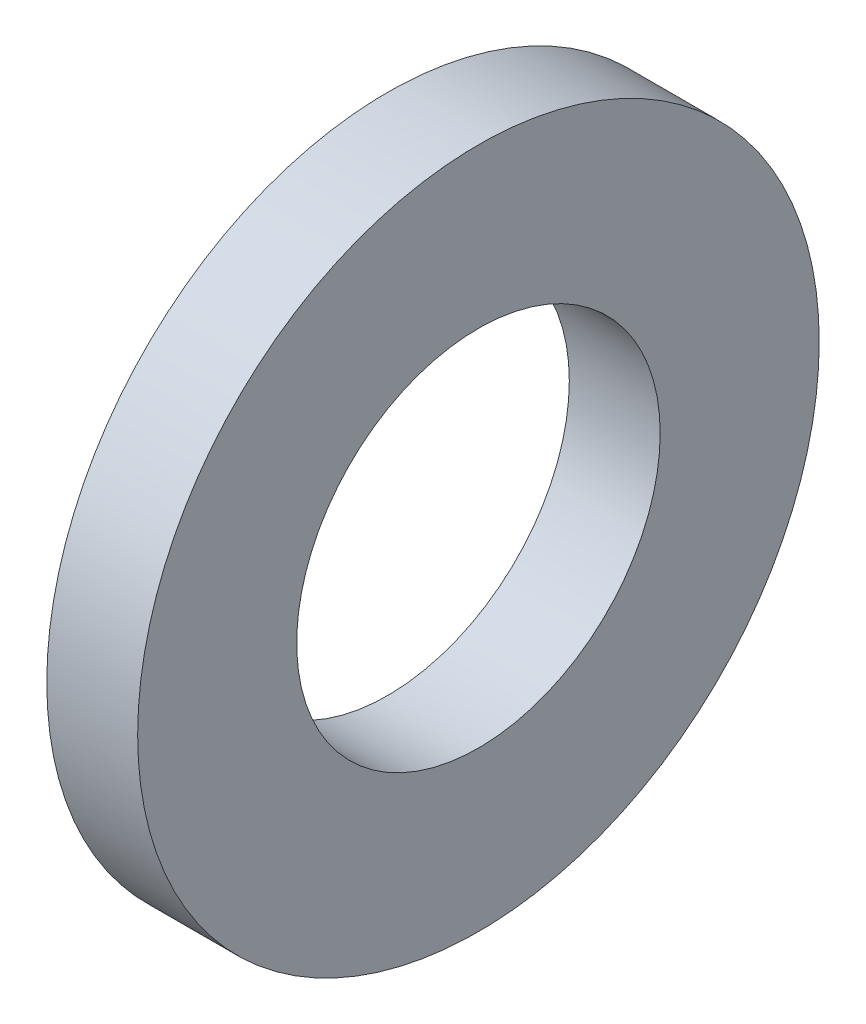
SolidWorks part; units mm, degrees
ref_plane "Płaszczyzna przednia" through (0, 0, 0) normal (0, 0, 1) x (1, 0, 0)
ref_plane "Płaszczyzna górna" through (0, 0, 0) normal (0, 1, 0) x (1, 0, 0)
ref_plane "Płaszczyzna prawa" through (0, 0, 0) normal (1, 0, 0) x (0, 0, -1)
sketch "Szkic1" plane through (0, 0, 0) normal (0, 0, 1) x (1, 0, 0)
  line L0 (0, 6) -> (0, 3.2)
  line L1 (0, 3.2) -> (1.6, 3.2)
  line L2 (1.6, 3.2) -> (1.6, 6)
  line L3 (1.6, 6) -> (0, 6)
  line L4 (0, 0) -> (1.6305, 0) construction
  dimension "D1" = 6
  dimension "D2" = 1.6
  dimension "D3" = 3.2
  dimension "D4" = 1.6305
revolve "Obrót1" add sketch "Szkic1" angle 360 about L4
